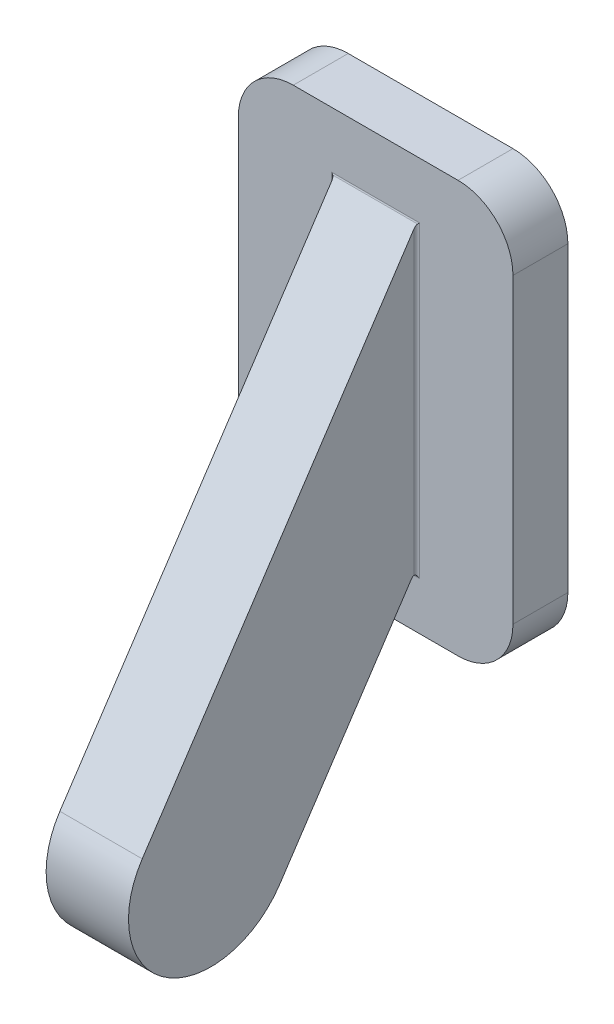
SolidWorks part; units mm, degrees
ref_plane "Front Plane" through (0, 0, 0) normal (0, 0, 1) x (1, 0, 0)
ref_plane "Top Plane" through (0, 0, 0) normal (0, 1, 0) x (1, 0, 0)
ref_plane "Right Plane" through (0, 0, 0) normal (1, 0, 0) x (0, 0, -1)
sketch "Sketch1" plane through (0, 0, 0) normal (0, 0, 1) x (1, 0, 0)
  line L1 (-5, -7.5) -> (5, -7.5)
  line L2 (-5, -7.5) -> (-5, 7.5)
  line L3 (-5, 7.5) -> (5, 7.5)
  line L4 (5, -7.5) -> (5, 7.5)
  line L5 (-5, -7.5) -> (5, 7.5) construction
  line L6 (-5, 7.5) -> (5, -7.5) construction
  point P0 (0, 0)
  dimension "D1" = 10
  dimension "D2" = 15
extrude "Boss-Extrude1" add sketch "Sketch1" along normal blind 2
sketch "Sketch3" plane through (0, 0, 0) normal (1, 0, 0) x (0, 0, -1)
  line L0 (-2, 5.4272) -> (-12, -9.6484)
  line L1 (-7, -12.965) -> (-2, -5.4272)
  line L2 (-2, -5.4272) -> (-2, 5.4272)
  line L3 (-2, -7.5) -> (-2, 7.5) construction
  arc A0 (-12, -9.6484) -> (-7, -12.965) centre (-9.5, -11.3067) ccw
  point P7 (-2, 0)
  dimension "D2" = 5
  dimension "D1" = 6
  dimension "D3" = 10
extrude "Boss-Extrude2" add sketch "Sketch3" along normal mid plane 3
fillet "Fillet1" radius 2 4 edges at (-5, 7.5, 1) (5, 7.5, 1) (5, -7.5, 1) (-5, -7.5, 1)
fillet "Fillet2" radius 0.1 4 edges at (-1.5, 0, 2) (0, -5.4272, 2) (0, 5.4272, 2) (1.5, 0, 2)
